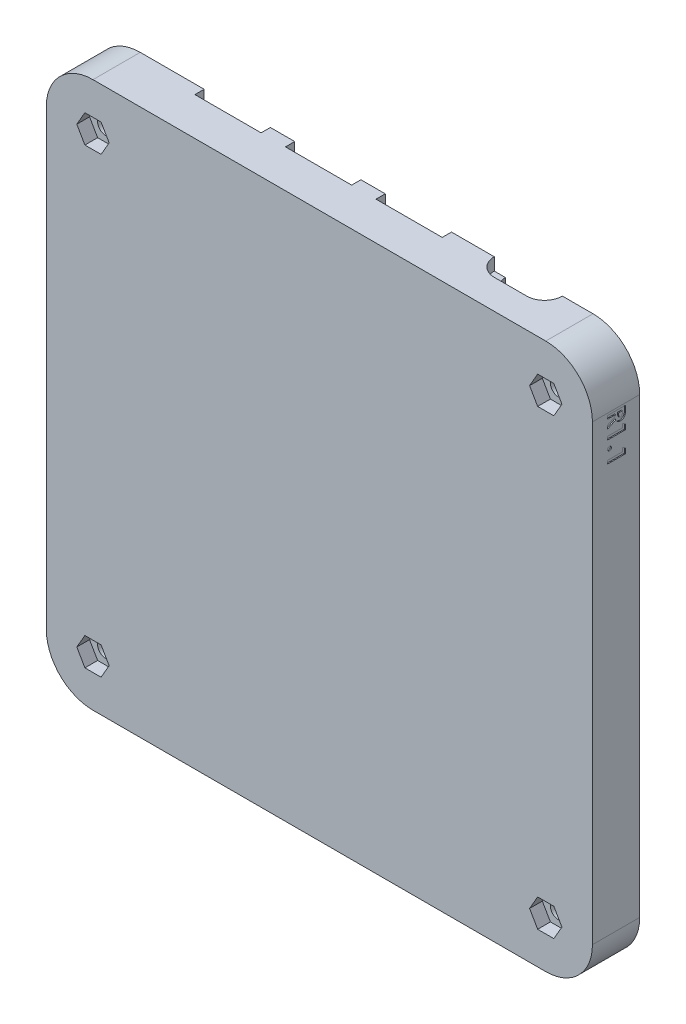
SolidWorks part; units mm, degrees
ref_plane "Front Plane" through (0, 0, 0) normal (0, 0, 1) x (1, 0, 0)
ref_plane "Top Plane" through (0, 0, 0) normal (0, 1, 0) x (1, 0, 0)
ref_plane "Right Plane" through (0, 0, 0) normal (1, 0, 0) x (0, 0, -1)
sketch "Sketch1" plane through (0, 0, 0) normal (0, 0, 1) x (1, 0, 0)
  circle A0 centre (-109.22, -20.32) radius 1.6 construction
  circle A1 centre (-109.22, -109.22) radius 1.6 construction
  circle A2 centre (-20.32, -109.22) radius 1.6 construction
  circle A3 centre (-20.32, -20.32) radius 1.6 construction
  circle A4 centre (-109.22, -20.32) radius 1.6
  circle A5 centre (-109.22, -109.22) radius 1.6
  circle A6 centre (-20.32, -109.22) radius 1.6
  circle A7 centre (-20.32, -20.32) radius 1.6
  circle A8 centre (-20.32, -20.32) radius 3.6
  circle A9 centre (-20.32, -109.22) radius 3.6
  circle A10 centre (-109.22, -109.22) radius 3.6
  circle A11 centre (-109.22, -20.32) radius 3.6
  dimension "D1" = 2
extrude "Boss-Extrude1" add sketch "Sketch1" along normal blind 3
ref_plane "Plane1" through (0, 0, -3.28) normal (0, 0, -1) x (-1, 0, 0)
sketch "Sketch2" plane through (0, 0, 3) normal (0, 0, 1) x (1, 0, 0)
  line L0 (-109.22, -114.4) -> (-20.32, -114.4)
  line L1 (-15.14, -109.22) -> (-15.14, -20.32)
  line L2 (-20.32, -15.14) -> (-109.22, -15.14)
  line L3 (-114.4, -20.32) -> (-114.4, -109.22)
  line L4 (-20.32, -11.156) -> (-109.22, -11.156)
  line L9 (-118.384, -20.32) -> (-118.384, -109.22)
  line L10 (-109.22, -118.384) -> (-20.32, -118.384)
  line L11 (-11.156, -109.22) -> (-11.156, -20.32)
  line L12 (-20.32, -15.24) -> (-109.22, -15.24)
  line L13 (-114.3, -20.32) -> (-114.3, -109.22)
  line L14 (-109.22, -114.3) -> (-20.32, -114.3)
  line L15 (-15.24, -109.22) -> (-15.24, -20.32)
  line L16 (-20.32, -15.24) -> (-109.22, -15.24) construction
  line L17 (-114.3, -20.32) -> (-114.3, -109.22) construction
  line L18 (-109.22, -114.3) -> (-20.32, -114.3) construction
  line L19 (-15.24, -109.22) -> (-15.24, -20.32) construction
  arc A0 (-20.32, -114.4) -> (-15.14, -109.22) centre (-20.32, -109.22) ccw
  arc A1 (-15.14, -20.32) -> (-20.32, -15.14) centre (-20.32, -20.32) ccw
  arc A2 (-109.22, -15.14) -> (-114.4, -20.32) centre (-109.22, -20.32) ccw
  arc A3 (-114.4, -109.22) -> (-109.22, -114.4) centre (-109.22, -109.22) ccw
  arc A8 (-109.22, -11.156) -> (-118.384, -20.32) centre (-109.22, -20.32) ccw
  arc A9 (-118.384, -109.22) -> (-109.22, -118.384) centre (-109.22, -109.22) ccw
  arc A10 (-20.32, -118.384) -> (-11.156, -109.22) centre (-20.32, -109.22) ccw
  arc A11 (-11.156, -20.32) -> (-20.32, -11.156) centre (-20.32, -20.32) ccw
  arc A12 (-15.24, -20.32) -> (-20.32, -15.24) centre (-20.32, -20.32) ccw
  arc A13 (-109.22, -15.24) -> (-114.3, -20.32) centre (-109.22, -20.32) ccw
  arc A14 (-114.3, -109.22) -> (-109.22, -114.3) centre (-109.22, -109.22) ccw
  arc A15 (-20.32, -114.3) -> (-15.24, -109.22) centre (-20.32, -109.22) ccw
  arc A16 (-15.24, -20.32) -> (-20.32, -15.24) centre (-20.32, -20.32) ccw construction
  arc A17 (-109.22, -15.24) -> (-114.3, -20.32) centre (-109.22, -20.32) ccw construction
  arc A18 (-114.3, -109.22) -> (-109.22, -114.3) centre (-109.22, -109.22) ccw construction
  arc A19 (-20.32, -114.3) -> (-15.24, -109.22) centre (-20.32, -109.22) ccw construction
  dimension "D1" = 0
  dimension "D2" = 0.1
extrude "Boss-Extrude2" add sketch "Sketch2" against normal up to surface (6.28 mm away) separate body up to plane "Plane1"
sketch "Sketch3" plane through (0, 0, 3) normal (0, 0, 1) x (1, 0, 0)
  line L0 (-109.22, -118.384) -> (-20.32, -118.384) construction
  line L1 (-11.156, -109.22) -> (-11.156, -20.32) construction
  line L2 (-20.32, -11.156) -> (-109.22, -11.156) construction
  line L3 (-118.384, -20.32) -> (-118.384, -109.22) construction
  line L4 (-11.156, -109.22) -> (-11.156, -20.32)
  line L5 (-20.32, -11.156) -> (-109.22, -11.156)
  line L6 (-118.384, -20.32) -> (-118.384, -109.22)
  line L7 (-109.22, -118.384) -> (-20.32, -118.384)
  arc A0 (-20.32, -118.384) -> (-11.156, -109.22) centre (-20.32, -109.22) ccw construction
  arc A1 (-11.156, -20.32) -> (-20.32, -11.156) centre (-20.32, -20.32) ccw construction
  arc A2 (-109.22, -11.156) -> (-118.384, -20.32) centre (-109.22, -20.32) ccw construction
  arc A3 (-118.384, -109.22) -> (-109.22, -118.384) centre (-109.22, -109.22) ccw construction
  arc A4 (-20.32, -118.384) -> (-11.156, -109.22) centre (-20.32, -109.22) ccw
  arc A5 (-11.156, -20.32) -> (-20.32, -11.156) centre (-20.32, -20.32) ccw
  arc A6 (-109.22, -11.156) -> (-118.384, -20.32) centre (-109.22, -20.32) ccw
  arc A7 (-118.384, -109.22) -> (-109.22, -118.384) centre (-109.22, -109.22) ccw
  circle A8 centre (-109.22, -109.22) radius 1.6 construction
  circle A9 centre (-20.32, -109.22) radius 1.6 construction
  circle A10 centre (-20.32, -20.32) radius 1.6 construction
  circle A11 centre (-109.22, -20.32) radius 1.6 construction
  circle A12 centre (-109.22, -109.22) radius 1.6
  circle A13 centre (-20.32, -109.22) radius 1.6
  circle A14 centre (-20.32, -20.32) radius 1.6
  circle A15 centre (-109.22, -20.32) radius 1.6
extrude "Boss-Extrude3" add sketch "Sketch3" along normal blind 3
sketch "Sketch5" plane through (0, -11.156, 0) normal (0, 1, 0) x (1, 0, 0)
  line L0 (-96.17, 1.861) -> (-96.17, 12.286) construction
  line L1 (-96.67, 12.761) -> (-83.67, 12.761)
  line L2 (-96.67, 12.761) -> (-96.67, 1.461)
  line L3 (-96.67, 1.461) -> (-83.67, 1.461)
  line L4 (-83.67, 12.761) -> (-83.67, 1.461)
  line L5 (-95.62, 12.336) -> (-84.72, 12.336) construction
  line L6 (-95.62, 12.561) -> (-84.72, 12.561) construction
  line L7 (-85.62, 1.561) -> (-94.72, 1.561) construction
  line L8 (-60.06, 12.336) -> (-49.16, 12.336) construction
  line L9 (-78.89, 12.761) -> (-78.89, 1.461)
  line L10 (-78.89, 12.761) -> (-65.89, 12.761)
  line L11 (-65.89, 12.761) -> (-65.89, 1.461)
  line L12 (-78.89, 1.461) -> (-65.89, 1.461)
  line L13 (-61.11, 12.761) -> (-61.11, 1.461)
  line L14 (-61.11, 12.761) -> (-48.11, 12.761)
  line L15 (-48.11, 12.761) -> (-48.11, 1.461)
  line L16 (-61.11, 1.461) -> (-48.11, 1.461)
  line L17 (-29.83, 1.7) -> (-33.265, 1.7) construction
  line L18 (-28.55, 2.98) -> (-28.55, 3.58) construction
  line L19 (-33.275, 1.7) -> (-36.21, 1.7) construction
  line L20 (-37.49, 3.58) -> (-37.49, 2.98) construction
  line L21 (-29.83, 4.86) -> (-36.21, 4.86) construction
  line L22 (-29.83, 1.7) -> (-33.265, 1.7)
  line L23 (-28.55, 2.98) -> (-28.55, 3.58)
  line L24 (-33.275, 1.7) -> (-36.21, 1.7)
  line L25 (-37.49, 3.58) -> (-37.49, 2.98)
  line L26 (-29.83, 4.86) -> (-36.21, 4.86)
  line L27 (-33.275, 1.7) -> (-33.265, 1.7)
  arc A0 (-29.83, 1.7) -> (-28.55, 2.98) centre (-29.83, 2.98) ccw construction
  arc A1 (-28.55, 3.58) -> (-29.83, 4.86) centre (-29.83, 3.58) ccw construction
  arc A2 (-37.49, 2.98) -> (-36.21, 1.7) centre (-36.21, 2.98) ccw construction
  arc A3 (-36.21, 4.86) -> (-37.49, 3.58) centre (-36.21, 3.58) ccw construction
  arc A4 (-29.83, 1.7) -> (-28.55, 2.98) centre (-29.83, 2.98) ccw
  arc A5 (-28.55, 3.58) -> (-29.83, 4.86) centre (-29.83, 3.58) ccw
  arc A6 (-37.49, 2.98) -> (-36.21, 1.7) centre (-36.21, 2.98) ccw
  arc A7 (-36.21, 4.86) -> (-37.49, 3.58) centre (-36.21, 3.58) ccw
  point P8 (-54.61, 12.761)
  point P9 (-90.17, 12.761)
  point P10 (-90.17, 12.336)
  point P15 (-54.61, 12.336)
  point P16 (-54.61, 12.336)
  dimension "D1" = 0.5
  dimension "D2" = 0.2
  dimension "D3" = 0.1
  dimension "D4" = 3
extrude "Cut-Extrude1" cut sketch "Sketch5" against normal up to next
sketch "Sketch7" plane through (0, -11.156, 0) normal (0, 1, 0) x (1, 0, 0)
  line L6 (-36.21, 3.58) -> (-36.21, 2.98) construction
  line L7 (-29.83, 2.98) -> (-29.83, 3.58) construction
  line L8 (-36.21, 3.28) -> (-29.83, 3.28) construction
  line L9 (-36.21, 6.78) -> (-29.83, 6.78)
  line L10 (-36.21, -0.22) -> (-29.83, -0.22)
  arc A4 (-36.21, 6.78) -> (-36.21, -0.22) centre (-36.21, 3.28) ccw
  arc A5 (-29.83, -0.22) -> (-29.83, 6.78) centre (-29.83, 3.28) ccw
  point P5 (-33.02, 3.28)
  dimension "D1" = 7
extrude "Cut-Extrude2" cut sketch "Sketch7" against normal up to surface (2.436 mm away)
sketch "Sketch8" plane through (-118.384, 0, 0) normal (-1, 0, 0) x (0, 0, 1)
  line L0 (-9.33, -83.7598) -> (-9.33, -73.0598) construction
  line L1 (-9.53, -85.7098) -> (-1.6, -85.7098)
  line L2 (-9.53, -85.7098) -> (-9.53, -71.1098)
  line L3 (-9.53, -71.1098) -> (-1.6, -71.1098)
  line L4 (-1.6, -85.7098) -> (-1.6, -71.1098)
  line L5 (-9.33, -43.1198) -> (-9.33, -32.4198) construction
  line L6 (-8.01, -85.6098) -> (-3.49, -85.6098) construction
  line L8 (-1.6, -109.22) -> (-1.6, -20.32) construction
  line L9 (-9.53, -65.3898) -> (-9.53, -50.7898)
  line L10 (-9.53, -65.3898) -> (-1.6, -65.3898)
  line L11 (-1.6, -65.3898) -> (-1.6, -50.7898)
  line L12 (-9.53, -50.7898) -> (-1.6, -50.7898)
  line L13 (-9.53, -45.0698) -> (-9.53, -30.4698)
  line L14 (-9.53, -45.0698) -> (-1.6, -45.0698)
  line L15 (-1.6, -45.0698) -> (-1.6, -30.4698)
  line L16 (-9.53, -30.4698) -> (-1.6, -30.4698)
  point P4 (-9.33, -78.4098)
  point P5 (-9.33, -37.7698)
  point P12 (-9.53, -78.4098)
  point P13 (-9.53, -37.7698)
  dimension "D1" = 0.2
  dimension "D2" = 0.1
  dimension "D3" = 3
extrude "Cut-Extrude3" cut sketch "Sketch8" against normal up to next
sketch "Sketch9" plane through (0, -118.384, 0) normal (0, -1, 0) x (-1, 0, 0)
  line L0 (56.82, 1.66) -> (56.82, 2.04) construction
  line L1 (55.82, 1.6) -> (66.1, 1.6)
  line L2 (55.82, 1.6) -> (55.82, 3.28)
  line L3 (55.82, 3.28) -> (66.1, 3.28)
  line L4 (66.1, 1.6) -> (66.1, 3.28)
  line L5 (65.1, 1.66) -> (65.1, 2.04) construction
  line L6 (56.82, 1.66) -> (56.82, 2.04) construction
  line L7 (65.1, 1.66) -> (65.1, 2.04) construction
  line L8 (18.8729, 1.6) -> (18.3729, 1.6) construction
  line L9 (56.82, 1.85) -> (65.1, 1.85) construction
  line L10 (109.22, 3.28) -> (20.32, 3.28) construction
  line L11 (103.2, 1.66) -> (103.2, 2.04) construction
  line L12 (94.92, 1.66) -> (94.92, 2.04) construction
  line L13 (103.2, 1.66) -> (103.2, 2.04) construction
  line L14 (94.92, 1.66) -> (94.92, 2.04) construction
  line L15 (94.92, 1.85) -> (103.2, 1.85) construction
  line L16 (68.52, 1.6) -> (68.52, 3.28)
  line L17 (68.52, 1.6) -> (78.8, 1.6)
  line L18 (78.8, 1.6) -> (78.8, 3.28)
  line L19 (68.52, 3.28) -> (78.8, 3.28)
  line L20 (81.22, 1.6) -> (81.22, 3.28)
  line L21 (81.22, 1.6) -> (91.5, 1.6)
  line L22 (91.5, 1.6) -> (91.5, 3.28)
  line L23 (81.22, 3.28) -> (91.5, 3.28)
  line L24 (93.92, 1.6) -> (93.92, 3.28)
  line L25 (93.92, 1.6) -> (104.2, 1.6)
  line L26 (104.2, 1.6) -> (104.2, 3.28)
  line L27 (93.92, 3.28) -> (104.2, 3.28)
  point P12 (60.96, 1.85)
  point P13 (60.96, 1.6)
  point P22 (99.06, 1.85)
  point P23 (99.06, 1.6)
  dimension "D1" = 1
  dimension "D2" = 4
extrude "Cut-Extrude4" cut sketch "Sketch9" against normal up to next
chamfer "Chamfer1" distance 1 angle 75 8 edges at (-91.5, -118.384, -2.44) (-93.92, -118.384, -2.44) (-104.2, -118.384, -2.44) (-81.22, -118.384, -2.44) (-78.8, -118.384, -2.44) (-68.52, -118.384, -2.44) (-66.1, -118.384, -2.44) (-55.82, -118.384, -2.44)
sketch "Sketch10" plane through (0, 0, 6) normal (0, 0, 1) x (1, 0, 0)
  line L1 (-23.4954, -109.22) -> (-21.9077, -111.97)
  line L2 (-21.9077, -111.97) -> (-18.7323, -111.97)
  line L3 (-18.7323, -111.97) -> (-17.1446, -109.22)
  line L4 (-17.1446, -109.22) -> (-18.7323, -106.47)
  line L5 (-18.7323, -106.47) -> (-21.9077, -106.47)
  line L6 (-21.9077, -106.47) -> (-23.4954, -109.22)
  line L7 (-106.0446, -109.22) -> (-107.6323, -106.47)
  line L8 (-107.6323, -106.47) -> (-110.8077, -106.47)
  line L9 (-110.8077, -106.47) -> (-112.3954, -109.22)
  line L10 (-112.3954, -109.22) -> (-110.8077, -111.97)
  line L11 (-110.8077, -111.97) -> (-107.6323, -111.97)
  line L12 (-107.6323, -111.97) -> (-106.0446, -109.22)
  line L13 (-106.0446, -20.32) -> (-107.6323, -17.57)
  line L14 (-107.6323, -17.57) -> (-110.8077, -17.57)
  line L15 (-110.8077, -17.57) -> (-112.3954, -20.32)
  line L16 (-112.3954, -20.32) -> (-110.8077, -23.07)
  line L17 (-110.8077, -23.07) -> (-107.6323, -23.07)
  line L18 (-107.6323, -23.07) -> (-106.0446, -20.32)
  line L19 (-23.4954, -20.32) -> (-21.9077, -23.07)
  line L20 (-21.9077, -23.07) -> (-18.7323, -23.07)
  line L21 (-18.7323, -23.07) -> (-17.1446, -20.32)
  line L22 (-17.1446, -20.32) -> (-18.7323, -17.57)
  line L23 (-18.7323, -17.57) -> (-21.9077, -17.57)
  line L24 (-21.9077, -17.57) -> (-23.4954, -20.32)
  circle A0 centre (-20.32, -109.22) radius 2.75 construction
  circle A1 centre (-109.22, -109.22) radius 2.75 construction
  circle A2 centre (-109.22, -20.32) radius 2.75 construction
  circle A3 centre (-20.32, -20.32) radius 2.75 construction
  dimension "D1" = 5.5
extrude "Cut-Extrude5" cut sketch "Sketch10" against normal blind 2.5
sketch "Sketch11" plane through (-11.156, 0, 0) normal (1, 0, 0) x (0, 0, -1)
  line L0 (-3, -20.32) -> (-3, -63.155) construction
  line L1 (-6, -20.32) -> (3.28, -20.32) construction
  line L2 (3.28, -63.155) -> (16.6, -63.155) construction
  line L4 (-6, -109.22) -> (-6, -20.32) construction
  text T0 "<b>R1.1</b>"
  dimension "D1" = 3
extrude "Cut-Extrude6" cut sketch "Sketch11" against normal blind 0.2
